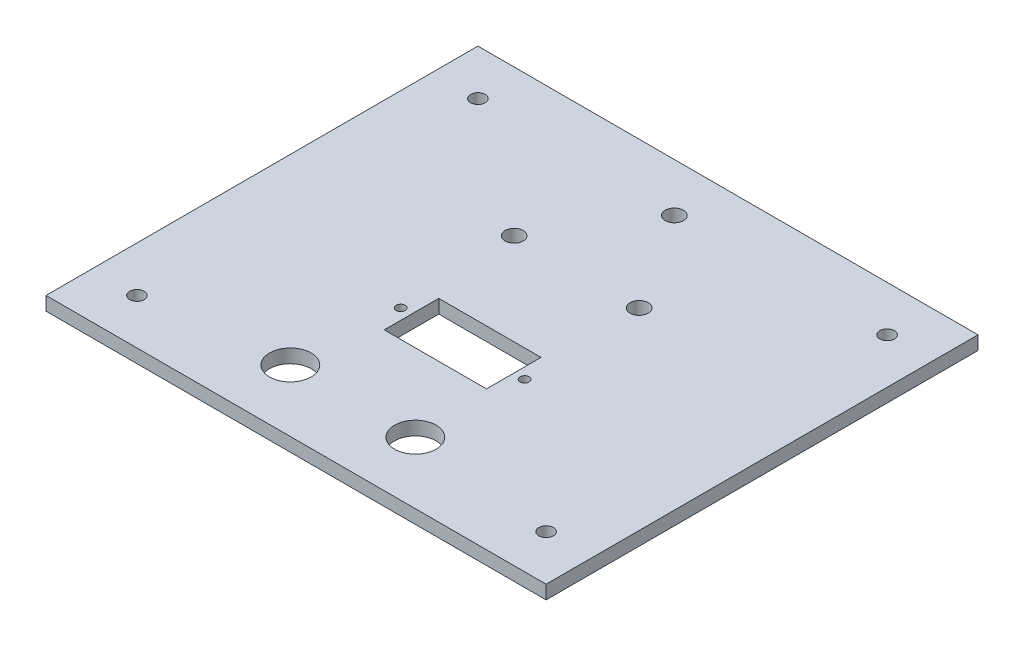
SolidWorks part; units mm, degrees
ref_plane "Front Plane" through (0, 0, 0) normal (0, 0, 1) x (1, 0, 0)
ref_plane "Top Plane" through (0, 0, 0) normal (0, 1, 0) x (1, 0, 0)
ref_plane "Right Plane" through (0, 0, 0) normal (1, 0, 0) x (0, 0, -1)
sketch "Sketch1" plane through (0, 0, 0) normal (0, 1, 0) x (1, 0, 0)
  line L0 (-55, 47.5) -> (55, -47.5)
  line L1 (-55, 47.5) -> (55, 47.5)
  line L2 (-55, 47.5) -> (-55, -47.5)
  line L3 (-55, -47.5) -> (55, -47.5)
  line L4 (55, 47.5) -> (55, -47.5)
  line L5 (55, 47.5) -> (-55, -47.5)
  line L6 (-1.135, 26.0556) -> (-1.135, 7.9735) construction
  circle A0 centre (-1.135, 36.8556) radius 2
  circle A1 centre (-14.885, 15.3556) radius 2
  circle A2 centre (12.615, 15.3556) radius 2
  point P4 (0, 0)
  dimension "D1" = 110
  dimension "D2" = 95
extrude "Boss-Extrude1" add sketch "Sketch1" along normal blind 3 contours L5 L1 L0 | L5 L0 L2 | L0 L5 L3 | L4 L5 L0
sketch "Sketch2" plane through (0, 3, 0) normal (0, 1, 0) x (1, 0, 0)
  line L0 (-55, 47.5) -> (-55, -47.5) construction
  line L1 (-55, 47.5) -> (55, 47.5) construction
  line L2 (55, 47.5) -> (55, -47.5) construction
  line L3 (-55, -47.5) -> (55, -47.5) construction
  circle A0 centre (-45, 37.5) radius 1.6
  circle A1 centre (45, 37.5) radius 1.6
  circle A2 centre (-45, -37.5) radius 1.6
  circle A3 centre (45, -37.5) radius 1.6
  dimension "D1" = 3.2
  dimension "D2" = 10
  dimension "D3" = 10
  dimension "D4" = 10
  dimension "D5" = 10
  dimension "D6" = 10
  dimension "D7" = 10
  dimension "D8" = 10
  dimension "D9" = 10
extrude "Cut-Extrude1" cut sketch "Sketch2" against normal blind 3
sketch "Sketch4" plane through (0, 3, 0) normal (0, 1, 0) x (1, 0, 0)
  line L0 (-14.885, 15.3556) -> (-14.885, -33.8697) construction
  line L1 (12.615, -33.8697) -> (12.615, 15.3556) construction
  line L2 (-14.885, -33.8697) -> (12.615, -33.8697) construction
  circle A0 centre (-14.885, -33.8697) radius 4.575
  circle A1 centre (12.615, -33.8697) radius 4.575
  dimension "D1" = 9.15
extrude "Cut-Extrude3" cut sketch "Sketch4" against normal blind 3 contours A0 | A1
sketch "Sketch5" plane through (0, 3, 0) normal (0, 1, 0) x (1, 0, 0)
  line L0 (-11.25, -4.8587) -> (11.25, -16.8587)
  line L1 (-11.25, -4.8587) -> (11.25, -4.8587)
  line L2 (-11.25, -4.8587) -> (-11.25, -16.8587)
  line L3 (-11.25, -16.8587) -> (11.25, -16.8587)
  line L4 (11.25, -4.8587) -> (11.25, -16.8587)
  line L5 (11.25, -4.8587) -> (-11.25, -16.8587)
  line L6 (-13.625, -10.8587) -> (13.625, -10.8587) construction
  circle A0 centre (-13.625, -10.8587) radius 1
  circle A1 centre (13.625, -10.8587) radius 1
  point P4 (0, -10.8587)
  dimension "D3" = 2
  dimension "D1" = 12
  dimension "D2" = 22.5
  dimension "D4" = 27.25
extrude "Cut-Extrude4" cut sketch "Sketch5" against normal blind 10
